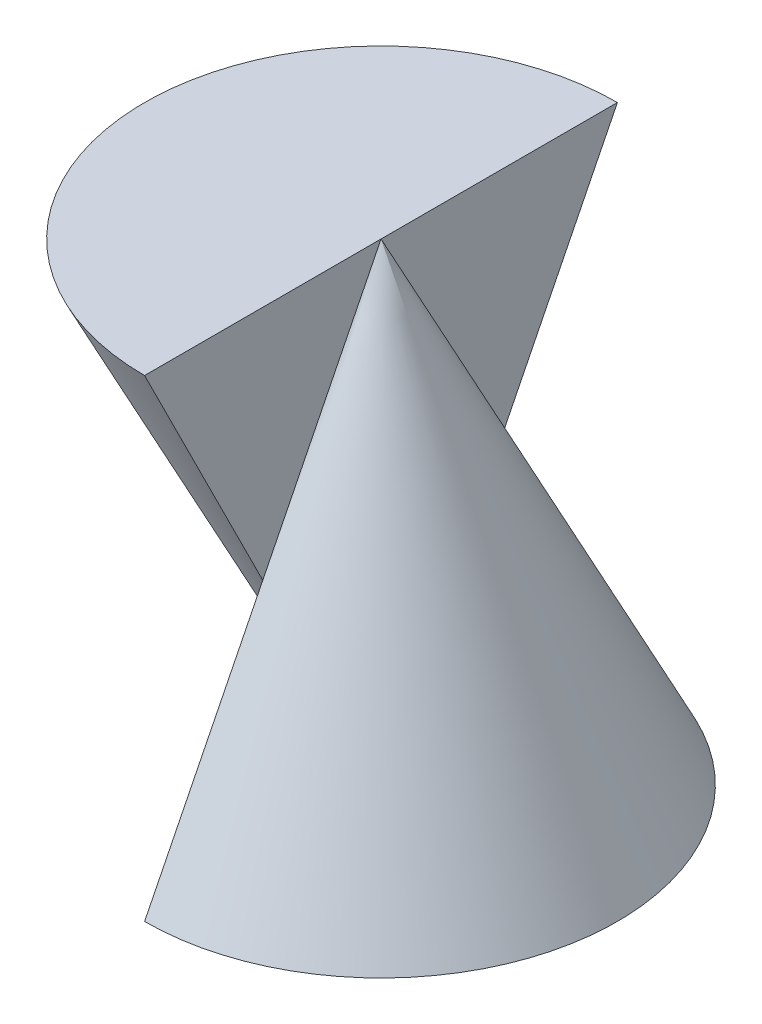
SolidWorks part; units mm, degrees
ref_plane "Front" through (0, 0, 0) normal (0, 0, 1) x (1, 0, 0)
ref_plane "Top" through (0, 0, 0) normal (0, 1, 0) x (1, 0, 0)
ref_plane "Right" through (0, 0, 0) normal (1, 0, 0) x (0, 0, -1)
sketch "Sketch1" plane through (0, 0, 0) normal (1, 0, 0) x (0, 0, -1)
  line L0 (0, 0) -> (0, 2.745) construction
  line L1 (0, 4) -> (-2, 0)
  line L2 (-2, 0) -> (0, 0)
  line L3 (0, 4) -> (0, 0)
  dimension "D1" = 2
  dimension "D2" = 4
revolve "Revolve1" add sketch "Sketch1" angle 180 about L0
sketch "Sketch2" plane through (0, 0, 0) normal (-1, 0, 0) x (0, 0, 1)
  line L0 (0, 4) -> (2, 4)
  line L1 (2, 4) -> (0, 0)
  line L2 (0, 0) -> (0, 4)
  dimension "D1" = 4
  dimension "D2" = 2
revolve "Revolve2" add sketch "Sketch2" angle 180 about L2
